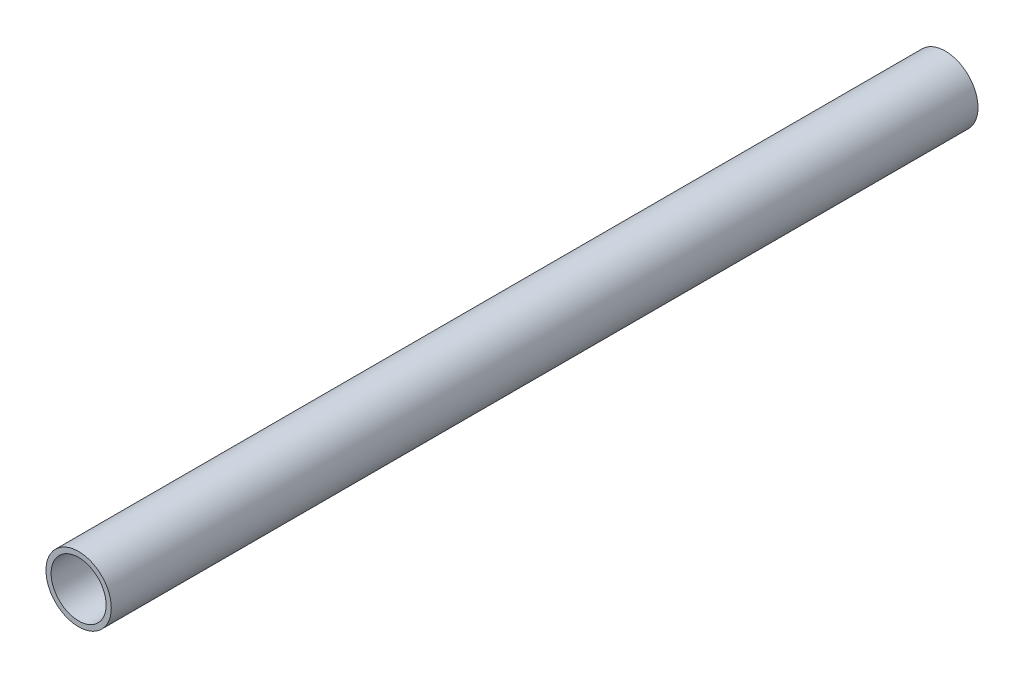
SolidWorks part; units mm, degrees
material "Balsa"
ref_plane "Front Plane" through (0, 0, 0) normal (0, 0, 1) x (1, 0, 0)
ref_plane "Top Plane" through (0, 0, 0) normal (0, 1, 0) x (1, 0, 0)
ref_plane "Right Plane" through (0, 0, 0) normal (1, 0, 0) x (0, 0, -1)
sketch "Sketch1" plane through (0, 0, 0) normal (0, 0, 1) x (1, 0, 0)
  circle A0 centre (0, 0) radius 8
  circle A1 centre (0, 0) radius 9.5
  dimension "D1" = 19
  dimension "D2" = 16
extrude "Boss-Extrude1" add sketch "Sketch1" along normal blind 252
